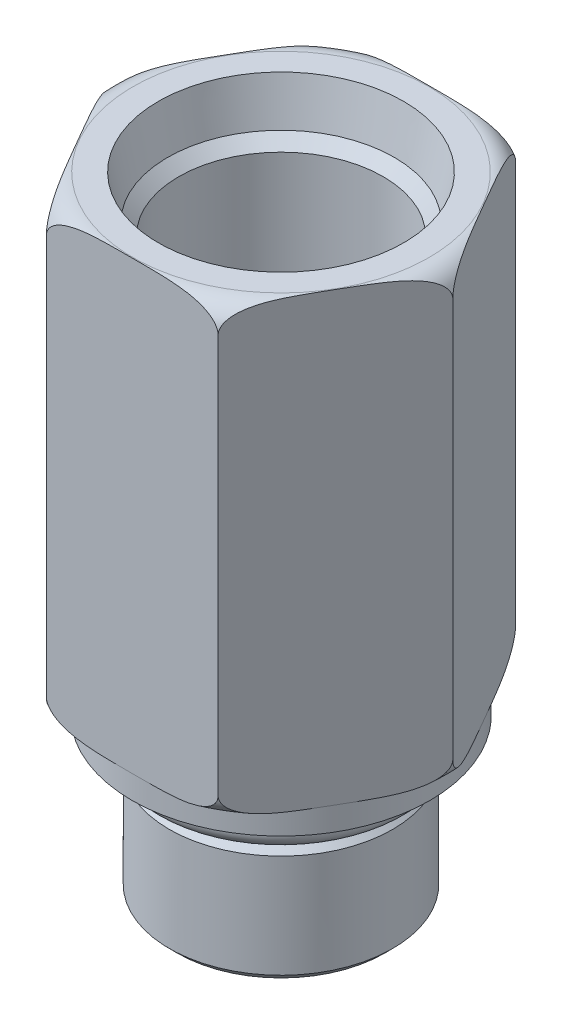
SolidWorks part; units mm, degrees
material "Alloy Steel"
ref_plane "Front Plane" through (0, 0, 0) normal (0, 0, 1) x (1, 0, 0)
ref_plane "Top Plane" through (0, 0, 0) normal (0, 1, 0) x (1, 0, 0)
ref_plane "Right Plane" through (0, 0, 0) normal (1, 0, 0) x (0, 0, -1)
ref_plane "Plane1" through (0, 0, 0) normal (0, 1, 0) x (1, 0, 0)
sketch "Sketch1" plane through (0, 0, 0) normal (0, 1, 0) x (1, 0, 0)
  line L8 (10.9985, 0) -> (5.4993, 9.525)
  line L9 (5.4993, 9.525) -> (-5.4993, 9.525)
  line L10 (-5.4993, 9.525) -> (-10.9985, 0)
  line L11 (-10.9985, 0) -> (-5.4993, -9.525)
  line L12 (-5.4993, -9.525) -> (5.4993, -9.525)
  line L13 (5.4993, -9.525) -> (10.9985, 0)
  circle A0 centre (0, 0) radius 9.525 construction
  dimension "D1" = 19.05
extrude "Extrude1" add sketch "Sketch1" along normal blind 28.575
ref_plane "Plane2" through (0, 0, 0) normal (0, 0, 1) x (1, 0, 0)
sketch "Sketch2" plane through (0, 0, 0) normal (0, 0, 1) x (1, 0, 0)
  line L0 (0, 26.9748) -> (0, 28.6512) construction
  line L1 (10.9985, 28.575) -> (9.4745, 28.575)
  line L4 (10.9985, 28.575) -> (10.9985, 0) construction
  line L5 (10.9985, 28.575) -> (10.9985, 27.051)
  arc A0 (10.9985, 27.051) -> (9.4745, 28.575) centre (9.4745, 27.051) ccw
  dimension "D1" = 1.524
revolve "Cut-Revolve1" cut sketch "Sketch2" angle 360 about L0
ref_plane "Plane3" through (0, 0, 0) normal (0, 0, 1) x (1, 0, 0)
sketch "Sketch3" plane through (0, 0, 0) normal (0, 0, 1) x (1, 0, 0)
  line L0 (0, -0.0762) -> (0, 1.6002) construction
  line L1 (10.9985, 0) -> (9.4745, 0)
  line L2 (10.9985, 0) -> (10.9985, 1.524)
  arc A0 (9.4745, 0) -> (10.9985, 1.524) centre (9.4745, 1.524) ccw
  dimension "D1" = 1.524
revolve "Cut-Revolve2" cut sketch "Sketch3" angle 360 about L0
ref_plane "Plane4" through (0, 28.575, 0) normal (0, 0, 1) x (1, 0, 0)
sketch "S2D0004" plane through (0, 28.575, 0) normal (0, 0, 1) x (1, 0, 0)
  line L0 (0, 0) -> (7.8486, 0)
  line L1 (7.8486, 0) -> (7.252, -2.8067)
  line L2 (7.252, -2.8067) -> (6.5405, -3.5182)
  line L3 (6.5405, -3.5182) -> (6.5405, -12.446)
  line L4 (6.5405, -12.446) -> (0, -12.446)
  line L5 (0, -12.446) -> (0, 0)
  line L6 (0, -28.575) -> (0, 0.6096) construction
  line L7 (9.4745, 0) -> (-9.4745, 0) construction
  dimension "D1" = 15.6972
  dimension "D2" = 12
  dimension "D3" = 45
  dimension "D4" = 2.8067
  dimension "D5" = 13.081
  dimension "D6" = 12.446
revolve "Cut-Revolve3" cut sketch "S2D0004" angle 360 about L6
ref_plane "Plane5" through (0, 0, 0) normal (0, 0, 1) x (1, 0, 0)
sketch "Sketch5" plane through (0, 0, 0) normal (0, 0, 1) x (1, 0, 0)
  line L0 (0, 0) -> (9.525, 0)
  line L1 (9.525, 0) -> (9.525, -1.4986)
  line L2 (9.525, -1.4986) -> (6.096, -1.4986)
  line L3 (6.096, -1.4986) -> (6.096, -3.7846)
  line L4 (6.096, -3.7846) -> (7.1437, -3.7846)
  line L5 (7.1437, -3.7846) -> (7.1438, -11.4046)
  line L6 (7.1438, -11.4046) -> (0, -11.4046)
  line L7 (0, -11.4046) -> (0, 0)
  line L8 (0, -14.9368) -> (0, 0.5055) construction
  line L9 (-9.4745, 0) -> (9.4745, 0) construction
  dimension "D1" = 9.906
  dimension "D2" = 11.4046
  dimension "D3" = 14.2875
  dimension "D4" = 12.192
  dimension "D5" = 2.286
  dimension "D6" = 19.05
revolve "Revolve1" add sketch "Sketch5" angle 360 about L8
chamfer "Chamfer1" distance 0.508 angle 45 2 edges at (0, -11.4046, -7.1438) (0, -3.7846, -7.1437)
ref_plane "Plane6" through (0, 0, 0) normal (0, 0, 1) x (1, 0, 0)
ref_plane "Plane7" through (0, 0, 0) normal (0, 0, 1) x (1, 0, 0)
sketch "Sketch7" plane through (0, 0, 0) normal (0, 0, 1) x (1, 0, 0)
  line L0 (0, -3.0886) -> (0, -1.077) construction
  line L1 (-9.525, -1.4986) -> (9.525, -1.4986) construction
  circle A0 centre (7.0866, -2.4892) radius 0.9906
  dimension "D1" = 1.9812
  dimension "D2" = 14.1732
revolve "Revolve3" add sketch "Sketch7" angle 360 about L0
sketch "Sketch8" plane through (0, -11.4046, 0) normal (0, -1, 0) x (1, 0, 0)
  line L8 (3.6662, 0) -> (1.8331, 3.175)
  line L9 (1.8331, 3.175) -> (-1.8331, 3.175)
  line L10 (-1.8331, 3.175) -> (-3.6662, 0)
  line L11 (-3.6662, 0) -> (-1.8331, -3.175)
  line L12 (-1.8331, -3.175) -> (1.8331, -3.175)
  line L13 (1.8331, -3.175) -> (3.6662, 0)
  circle A0 centre (0, 0) radius 3.175 construction
  dimension "D1" = 6.35
extrude "Cut-Extrude1" cut sketch "Sketch8" against normal blind 9.906
